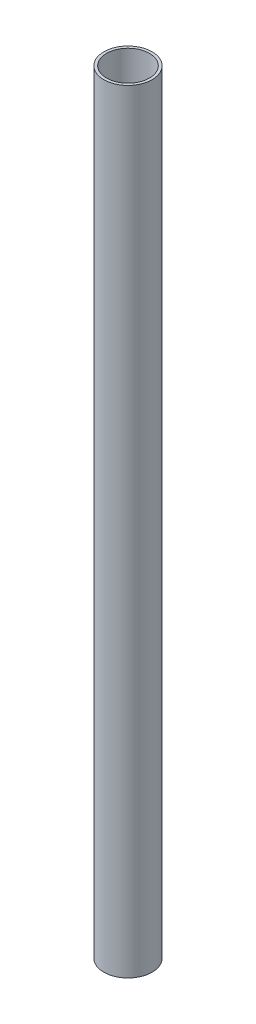
SolidWorks part; units mm, degrees
ref_plane "Front Plane" through (0, 0, 0) normal (0, 0, 1) x (1, 0, 0)
ref_plane "Top Plane" through (0, 0, 0) normal (0, 1, 0) x (1, 0, 0)
ref_plane "Right Plane" through (0, 0, 0) normal (1, 0, 0) x (0, 0, -1)
sketch "Sketch1" plane through (0, 0, 0) normal (0, 1, 0) x (1, 0, 0)
  circle A0 centre (0, 0) radius 6.35
  circle A1 centre (0, 0) radius 5.6388
  dimension "D1" = 12.7
  dimension "D2" = 11.2776
extrude "Boss-Extrude1" add sketch "Sketch1" along normal blind 203.2
